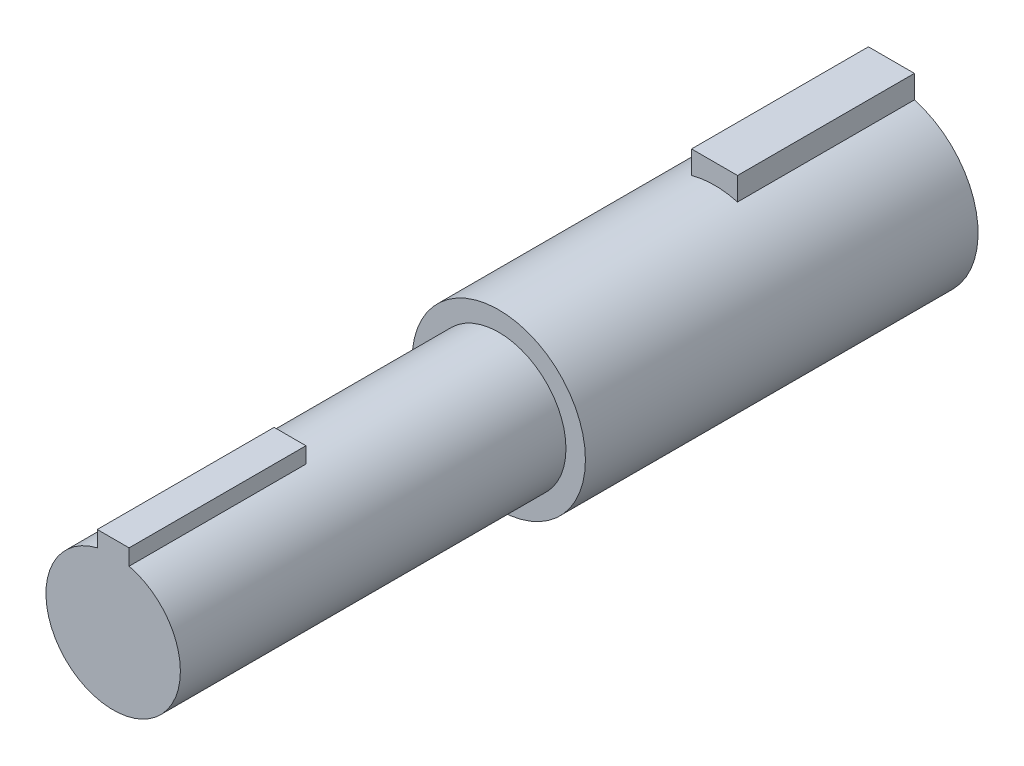
SolidWorks part; units mm, degrees
material "AISI 1020"
ref_plane "Front Plane" through (0, 0, 0) normal (0, 0, 1) x (1, 0, 0)
ref_plane "Top Plane" through (0, 0, 0) normal (0, 1, 0) x (1, 0, 0)
ref_plane "Right Plane" through (0, 0, 0) normal (1, 0, 0) x (0, 0, -1)
sketch "Sketch1" plane through (0, 0, 0) normal (0, 0, 1) x (1, 0, 0)
  circle A0 centre (0, 0) radius 6.223
  dimension "D1" = 12.446
extrude "Boss-Extrude1" add sketch "Sketch1" along normal blind 28.194
sketch "Sketch2" plane through (0, 0, 28.194) normal (0, 0, 1) x (1, 0, 0)
  circle A0 centre (0, 0) radius 4.826
  dimension "D1" = 9.652
extrude "Boss-Extrude2" add sketch "Sketch2" along normal blind 27.686 and the other way blind 5.08
sketch "Sketch3" plane through (0, 0, 55.88) normal (0, 0, 1) x (1, 0, 0)
  line L1 (-1.143, 5.8317) -> (1.143, 5.8317)
  line L2 (-1.143, 5.8317) -> (-1.143, 3.5457)
  line L3 (-1.143, 3.5457) -> (1.143, 3.5457)
  line L4 (1.143, 5.8317) -> (1.143, 3.5457)
  circle A0 centre (0, 0) radius 4.826 construction
  point P4 (0, 3.5457)
  point P6 (-1.143, 4.6887)
  dimension "D1" = 2.286
  dimension "D2" = 2.286
extrude "Boss-Extrude3" add sketch "Sketch3" against normal blind 12.7
sketch "Sketch4" plane through (0, 0, 0) normal (0, 0, -1) x (-1, 0, 0)
  line L1 (-1.651, 7.651) -> (1.651, 7.651)
  line L2 (-1.651, 7.651) -> (-1.651, 4.349)
  line L3 (-1.651, 4.349) -> (1.651, 4.349)
  line L4 (1.651, 7.651) -> (1.651, 4.349)
  circle A0 centre (0, 0) radius 6.223 construction
  point P4 (0, 4.349)
  point P6 (-1.651, 6)
  dimension "D1" = 3.302
  dimension "D2" = 3.302
extrude "Boss-Extrude4" add sketch "Sketch4" against normal blind 12.7
